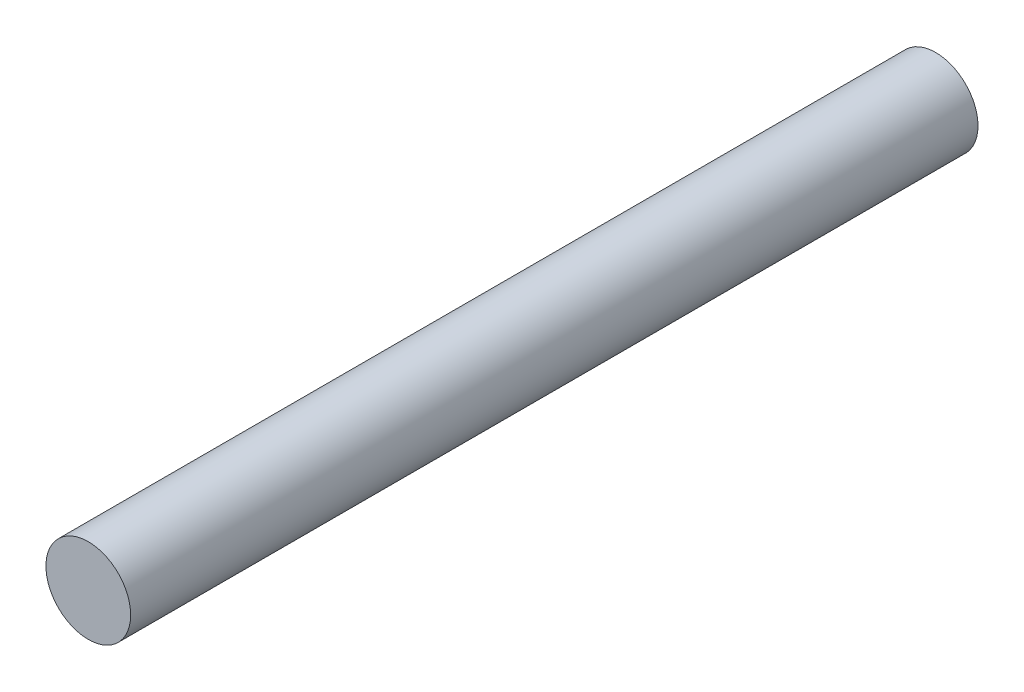
SolidWorks part; units mm, degrees
ref_plane "正面" through (0, 0, 0) normal (0, 0, 1) x (1, 0, 0)
ref_plane "平面" through (0, 0, 0) normal (0, 1, 0) x (1, 0, 0)
ref_plane "右側面" through (0, 0, 0) normal (1, 0, 0) x (0, 0, -1)
sketch "ｽｹｯﾁ1" plane through (0, 0, 0) normal (0, 0, 1) x (1, 0, 0)
  circle A0 centre (0, 0) radius 1.5
  dimension "D1" = 3
extrude "ﾎﾞｽ - 押し出し1" add sketch "ｽｹｯﾁ1" along normal blind 30
